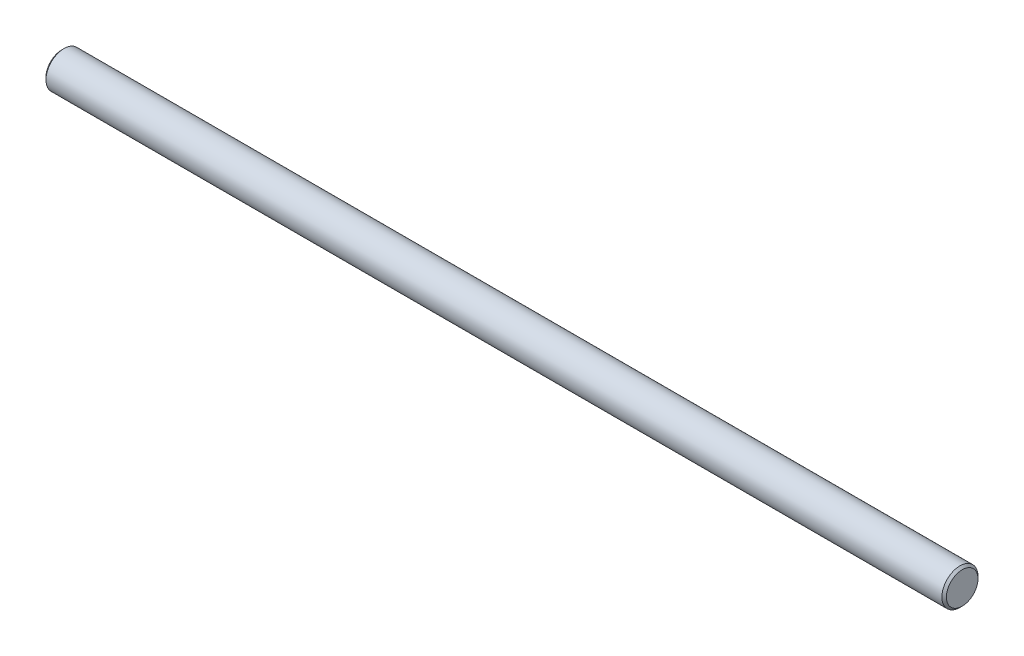
SolidWorks part; units mm, degrees
ref_plane "Front Plane" through (0, 0, 0) normal (0, 0, 1) x (1, 0, 0)
ref_plane "Top Plane" through (0, 0, 0) normal (0, 1, 0) x (1, 0, 0)
ref_plane "Right Plane" through (0, 0, 0) normal (1, 0, 0) x (0, 0, -1)
sketch "Sketch1" plane through (0, 0, 0) normal (1, 0, 0) x (0, 0, -1)
  circle A0 centre (0, 0) radius 4
  dimension "D1" = 8
extrude "Boss-Extrude1" add sketch "Sketch1" along normal blind 199.5
chamfer "Chamfer1" distance 0.5 angle 45 2 edges at (199.5, 0, -4) (0, 0, -4)
